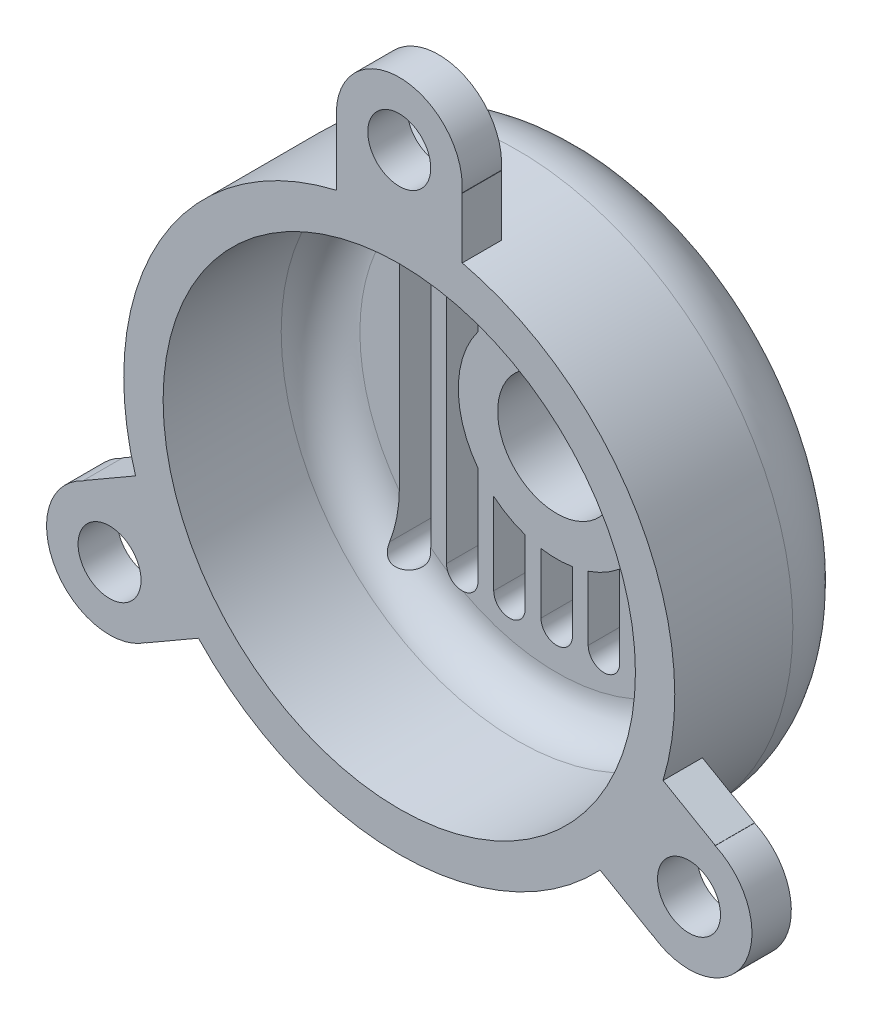
SolidWorks part; units mm, degrees
ref_plane "Front Plane" through (0, 0, 0) normal (0, 0, 1) x (1, 0, 0)
ref_plane "Top Plane" through (0, 0, 0) normal (0, 1, 0) x (1, 0, 0)
ref_plane "Right Plane" through (0, 0, 0) normal (1, 0, 0) x (0, 0, -1)
sketch "Sketch1" plane through (0, 0, 0) normal (0, 1, 0) x (1, 0, 0)
  line L0 (0, 0) -> (25, 0)
  line L1 (35, -10) -> (35, -25)
  line L2 (35, -25) -> (30, -25)
  line L3 (0, 0) -> (0, -5)
  line L4 (0, -5) -> (25, -5)
  line L5 (30, -25) -> (30, -10)
  line L6 (0, 16.9611) -> (0, -27.2529) construction
  arc A0 (25, 0) -> (35, -10) centre (25, -10) cw
  arc A1 (25, -5) -> (30, -10) centre (25, -10) cw
  dimension "D1" = 10
revolve "Revolve1" add sketch "Sketch1" angle 360 about L6
ref_plane "Plane1" through (0, 0, 25) normal (0, 0, 1) x (1, 0, 0)
sketch "Sketch3" plane through (0, 0, 25) normal (0, 0, 1) x (1, 0, 0)
  line L0 (40.8061, -14.3218) -> (33.5085, -10.1085)
  line L1 (32.8061, -28.1782) -> (25.5085, -23.9649)
  line L2 (-8, 42.5) -> (-8, 34.0735)
  line L3 (8, 42.5) -> (8, 34.0735)
  line L4 (-32.8061, -28.1782) -> (-25.5085, -23.9649)
  line L5 (-40.8061, -14.3218) -> (-33.5085, -10.1085)
  arc A0 (-40.1481, -13.9419) -> (-40.1363, -13.9761) centre (0, 0) ccw
  circle A1 centre (0, 42.5) radius 4
  arc A2 (7.9645, 41.7471) -> (-7.9645, 41.7471) centre (0, 42.5) ccw
  circle A3 centre (0, 0) radius 35 construction
  arc A4 (32.1718, -27.771) -> (40.1363, -13.9761) centre (36.8061, -21.25) ccw
  circle A5 centre (36.8061, -21.25) radius 4
  arc A6 (-40.1363, -13.9761) -> (-32.1718, -27.771) centre (-36.8061, -21.25) ccw
  circle A7 centre (-36.8061, -21.25) radius 4
  arc A8 (-32.1718, -27.771) -> (-32.1481, -27.7983) centre (0, 0) ccw
  arc A9 (40.1363, -13.9761) -> (40.1481, -13.9419) centre (0, 0) ccw
  arc A10 (32.1481, -27.7983) -> (32.1718, -27.771) centre (0, 0) ccw
  arc A11 (8, 41.7403) -> (7.9645, 41.7471) centre (0, 0) ccw
  circle A12 centre (0, 0) radius 35
  arc A13 (-7.9645, 41.7471) -> (-8, 41.7403) centre (0, 0) ccw
  point P31 (0, 0)
  dimension "D1" = 3
extrude "Boss-Extrude1" add sketch "Sketch3" against normal blind 5 contours A2 A13 L2 A12 L3 A11 A1 | A12 L5 A0 A6 A8 L4 A7 | A12 L1 A10 A4 A9 L0 A5
ref_plane "Plane2" through (0, 0, 0) normal (0, 0, 1) x (1, 0, 0)
sketch "Sketch5" plane through (0, 0, 0) normal (0, 0, 1) x (1, 0, 0)
  line L0 (0, 20) -> (0, -20) construction
  line L1 (2, 20) -> (2, -20)
  line L2 (-2, 20) -> (-2, -20)
  line L3 (6, 20) -> (6, -20) construction
  line L4 (8, 20) -> (8, -20)
  line L5 (4, 20) -> (4, -20)
  line L6 (12, 20) -> (12, -20) construction
  line L7 (14, 20) -> (14, -20)
  line L8 (10, 20) -> (10, -20)
  line L9 (18, 20) -> (18, -20) construction
  line L10 (20, 20) -> (20, -20)
  line L11 (16, 20) -> (16, -20)
  line L12 (0, 0) -> (0, 30.1126) construction
  line L13 (0, 30.1126) -> (0, -27.5974) construction
  line L14 (-12, 20) -> (-12, -20) construction
  line L15 (-14, 20) -> (-14, -20)
  line L16 (-10, 20) -> (-10, -20)
  line L17 (-6, 20) -> (-6, -20) construction
  line L18 (-8, 20) -> (-8, -20)
  line L19 (-4, 20) -> (-4, -20)
  line L20 (-18, 20) -> (-18, -20) construction
  line L21 (-20, 20) -> (-20, -20)
  line L22 (-16, 20) -> (-16, -20)
  arc A0 (2, 20) -> (-2, 20) centre (0, 20) ccw
  arc A1 (-2, -20) -> (2, -20) centre (0, -20) ccw
  arc A2 (8, 20) -> (4, 20) centre (6, 20) ccw
  arc A3 (4, -20) -> (8, -20) centre (6, -20) ccw
  arc A4 (14, 20) -> (10, 20) centre (12, 20) ccw
  arc A5 (10, -20) -> (14, -20) centre (12, -20) ccw
  arc A6 (20, 20) -> (16, 20) centre (18, 20) ccw
  arc A7 (16, -20) -> (20, -20) centre (18, -20) ccw
  arc A8 (-14, 20) -> (-10, 20) centre (-12, 20) cw
  arc A9 (-10, -20) -> (-14, -20) centre (-12, -20) cw
  arc A10 (-8, 20) -> (-4, 20) centre (-6, 20) cw
  arc A11 (-4, -20) -> (-8, -20) centre (-6, -20) cw
  arc A12 (-20, 20) -> (-16, 20) centre (-18, 20) cw
  arc A13 (-16, -20) -> (-20, -20) centre (-18, -20) cw
  point P2 (0, 0)
  point P11 (6, 0)
  point P18 (12, 0)
  point P25 (18, 0)
  point P35 (-12, 0)
  point P42 (-6, 0)
  point P49 (-18, 0)
  dimension "D2" = 2
  dimension "D1" = 40
  dimension "D3" = 4
extrude "Cut-Extrude1" cut sketch "Sketch5" along normal blind 80
ref_plane "Plane3" through (0, 0, 5) normal (0, 0, 1) x (1, 0, 0)
sketch "Sketch8" plane through (0, 0, 5) normal (0, 0, 1) x (1, 0, 0)
  circle A0 centre (0, 0) radius 7.5
  circle A1 centre (0, 0) radius 12.5
extrude "Boss-Extrude2" add sketch "Sketch8" against normal blind 10
fillet "Fillet1" radius 2 1 edges at (12.5, 0, -5)
sketch "Sketch9" plane through (0, 0, 0) normal (0, 0, 1) x (1, 0, 0)
  circle A0 centre (0, 0) radius 7.5
extrude "Cut-Extrude2" cut sketch "Sketch9" along normal blind 46
